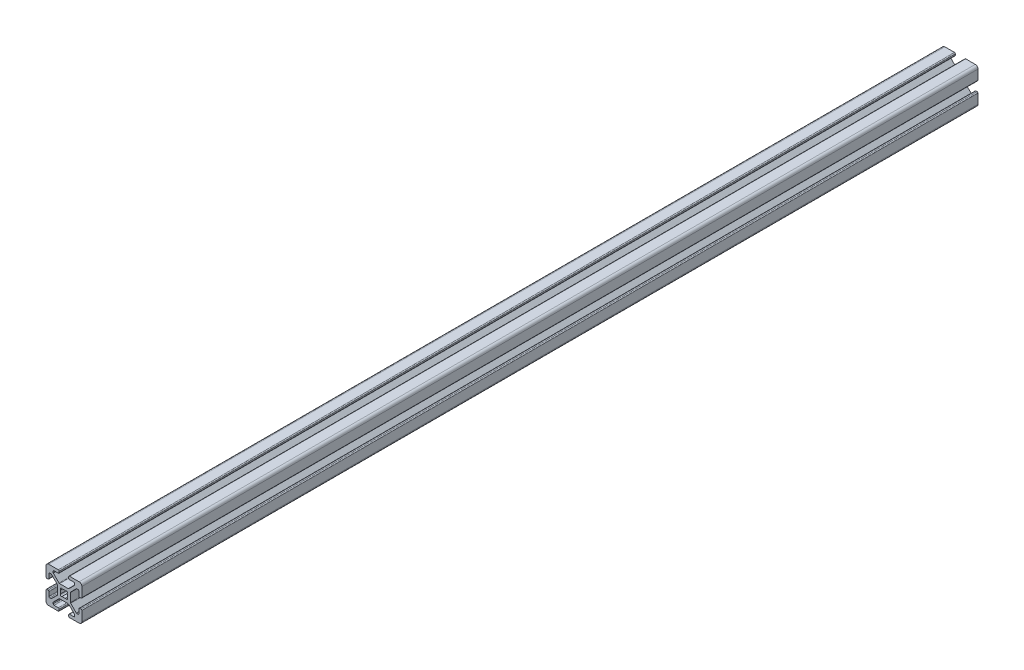
SolidWorks part; units mm, degrees
ref_plane "Front Plane" through (0, 0, 0) normal (0, 0, 1) x (1, 0, 0)
ref_plane "Top Plane" through (0, 0, 0) normal (0, 1, 0) x (1, 0, 0)
ref_plane "Right Plane" through (0, 0, 0) normal (1, 0, 0) x (0, 0, -1)
sketch "Sketch1" plane through (0, 0, 0) normal (0, 0, 1) x (1, 0, 0)
  line L0 (-2.7464, -3.807) -> (-5.848, -6.9086)
  line L1 (-8.5, -10) -> (-3.1319, -10)
  line L2 (-10, -8.5) -> (-10, -3.1319)
  line L3 (-8.5, 10) -> (-3.1319, 10)
  line L4 (10, -8.5) -> (10, -3.1319)
  line L6 (-10, 10) -> (-8.36, 8.36) construction
  line L7 (-2.3914, -3.66) -> (2.3914, -3.66)
  line L8 (-3.66, -2.3914) -> (-3.66, 2.3914)
  line L9 (-2.3914, 3.66) -> (2.3914, 3.66)
  line L10 (3.66, -2.3914) -> (3.66, 2.3914)
  line L13 (-5.4931, -8.36) -> (-3.1319, -8.36)
  line L14 (2.7464, -3.807) -> (5.848, -6.9086)
  line L15 (3.807, -2.7464) -> (6.9086, -5.848)
  line L16 (-5.995, -14.365) -> (5.995, -14.365)
  line L17 (2.63, -9.4981) -> (2.63, -8.8619)
  line L18 (8.8619, -2.63) -> (9.4981, -2.63)
  line L19 (5.995, -7.8581) -> (5.995, -7.2636)
  line L20 (-10, 3.1319) -> (-10, 8.5)
  line L22 (7.2636, -5.995) -> (7.8581, -5.995)
  line L23 (8.36, -5.4931) -> (8.36, -3.1319)
  line L24 (-3.807, -2.7464) -> (-6.9086, -5.848)
  line L25 (-9.4981, -2.63) -> (-8.8619, -2.63)
  line L26 (-7.8581, -5.995) -> (-7.2636, -5.995)
  line L27 (-5.995, -7.2636) -> (-5.995, -7.8581)
  line L28 (-2.63, -8.8619) -> (-2.63, -9.4981)
  line L30 (-5.4931, -8.36) -> (-3.1319, -8.36)
  line L31 (-3.807, 2.7464) -> (-6.9086, 5.848)
  line L32 (-2.7464, 3.807) -> (-5.848, 6.9086)
  line L33 (-2.63, 9.4981) -> (-2.63, 8.8619)
  line L34 (-5.995, 7.8581) -> (-5.995, 7.2636)
  line L35 (-7.2636, 5.995) -> (-7.8581, 5.995)
  line L36 (-8.8619, 2.63) -> (-9.4981, 2.63)
  line L37 (3.1319, 10) -> (8.5, 10)
  line L38 (-8.36, 5.4931) -> (-8.36, 3.1319)
  line L39 (2.7464, 3.807) -> (5.848, 6.9086)
  line L40 (3.807, 2.7464) -> (6.9086, 5.848)
  line L41 (9.4981, 2.63) -> (8.8619, 2.63)
  line L42 (7.8581, 5.995) -> (7.2636, 5.995)
  line L43 (5.995, 7.2636) -> (5.995, 7.8581)
  line L44 (2.63, 8.8619) -> (2.63, 9.4981)
  line L45 (8.36, -5.4931) -> (8.36, -3.1319)
  line L46 (5.4931, 8.36) -> (3.1319, 8.36)
  line L49 (-8.36, 5.4931) -> (-8.36, 3.1319)
  line L50 (5.4931, 8.36) -> (3.1319, 8.36)
  line L51 (-3.1319, 8.36) -> (-5.4931, 8.36)
  line L52 (-3.1319, 8.36) -> (-5.4931, 8.36)
  line L53 (10, 8.36) -> (8.36, 8.36) [skipped]
  line L54 (10, 3.1319) -> (10, 8.5)
  line L55 (8.36, 3.1319) -> (8.36, 5.4931)
  line L56 (8.36, 3.1319) -> (8.36, 5.4931)
  line L57 (3.1319, -8.36) -> (5.4931, -8.36)
  line L58 (3.1319, -8.36) -> (5.4931, -8.36)
  line L59 (3.1319, -10) -> (8.5, -10)
  line L60 (-8.36, -3.1319) -> (-8.36, -5.4931)
  line L61 (-8.36, -3.1319) -> (-8.36, -5.4931)
  line L62 (-8.36, 10) -> (-8.36, 8.36) [skipped]
  arc A0 (-8.5, -10) -> (-10, -8.5) centre (-8.5, -8.5) cw
  arc A1 (8.5, -10) -> (10, -8.5) centre (8.5, -8.5) ccw
  arc A2 (10, 8.5) -> (8.5, 10) centre (8.5, 8.5) ccw
  arc A3 (-8.5, 10) -> (-10, 8.5) centre (-8.5, 8.5) ccw
  arc A4 (10, -3.1319) -> (9.4981, -2.63) centre (9.4981, -3.1319) ccw
  arc A5 (8.8619, -2.63) -> (8.36, -3.1319) centre (8.8619, -3.1319) ccw
  arc A6 (7.8581, -5.995) -> (8.36, -5.4931) centre (7.8581, -5.4931) ccw
  arc A7 (7.2636, -5.995) -> (6.9086, -5.848) centre (7.2636, -5.4931) cw
  arc A8 (5.995, -7.2636) -> (5.848, -6.9086) centre (5.4931, -7.2636) ccw
  arc A9 (5.995, -7.8581) -> (5.4931, -8.36) centre (5.4931, -7.8581) cw
  arc A10 (3.1319, -10) -> (2.63, -9.4981) centre (3.1319, -9.4981) cw
  arc A11 (2.63, -8.8619) -> (3.1319, -8.36) centre (3.1319, -8.8619) cw
  arc A12 (-3.1319, -10) -> (-2.63, -9.4981) centre (-3.1319, -9.4981) ccw
  arc A13 (-2.63, -8.8619) -> (-3.1319, -8.36) centre (-3.1319, -8.8619) ccw
  arc A14 (-5.4931, -8.36) -> (-5.995, -7.8581) centre (-5.4931, -7.8581) cw
  arc A15 (-5.995, -7.2636) -> (-5.848, -6.9086) centre (-5.4931, -7.2636) cw
  arc A16 (-9.4981, -2.63) -> (-10, -3.1319) centre (-9.4981, -3.1319) ccw
  arc A17 (-8.36, -3.1319) -> (-8.8619, -2.63) centre (-8.8619, -3.1319) ccw
  arc A18 (-7.2636, -5.995) -> (-6.9086, -5.848) centre (-7.2636, -5.4931) ccw
  arc A19 (-7.8581, -5.995) -> (-8.36, -5.4931) centre (-7.8581, -5.4931) cw
  arc A20 (-3.807, -2.7464) -> (-3.66, -2.3914) centre (-4.1619, -2.3914) ccw
  arc A21 (-2.3914, -3.66) -> (-2.7464, -3.807) centre (-2.3914, -4.1619) ccw
  arc A22 (2.7464, -3.807) -> (2.3914, -3.66) centre (2.3914, -4.1619) ccw
  arc A23 (3.807, -2.7464) -> (3.66, -2.3914) centre (4.1619, -2.3914) cw
  arc A24 (9.4981, 2.63) -> (10, 3.1319) centre (9.4981, 3.1319) ccw
  arc A25 (8.8619, 2.63) -> (8.36, 3.1319) centre (8.8619, 3.1319) cw
  arc A26 (5.848, 6.9086) -> (5.995, 7.2636) centre (5.4931, 7.2636) ccw
  arc A27 (7.2636, 5.995) -> (6.9086, 5.848) centre (7.2636, 5.4931) ccw
  arc A28 (8.36, 5.4931) -> (7.8581, 5.995) centre (7.8581, 5.4931) ccw
  arc A29 (5.995, 7.8581) -> (5.4931, 8.36) centre (5.4931, 7.8581) ccw
  arc A30 (3.66, 2.3914) -> (3.807, 2.7464) centre (4.1619, 2.3914) cw
  arc A31 (-3.66, 2.3914) -> (-3.807, 2.7464) centre (-4.1619, 2.3914) ccw
  arc A32 (2.3914, 3.66) -> (2.7464, 3.807) centre (2.3914, 4.1619) ccw
  arc A33 (-2.3914, 3.66) -> (-2.7464, 3.807) centre (-2.3914, 4.1619) cw
  arc A34 (3.1319, 8.36) -> (2.63, 8.8619) centre (3.1319, 8.8619) cw
  arc A35 (2.63, 9.4981) -> (3.1319, 10) centre (3.1319, 9.4981) cw
  arc A36 (-9.4981, 2.63) -> (-10, 3.1319) centre (-9.4981, 3.1319) cw
  arc A37 (-8.8619, 2.63) -> (-8.36, 3.1319) centre (-8.8619, 3.1319) ccw
  arc A38 (-3.1319, 8.36) -> (-2.63, 8.8619) centre (-3.1319, 8.8619) ccw
  arc A39 (-2.63, 9.4981) -> (-3.1319, 10) centre (-3.1319, 9.4981) ccw
  arc A40 (-5.848, 6.9086) -> (-5.995, 7.2636) centre (-5.4931, 7.2636) cw
  arc A41 (-5.4931, 8.36) -> (-5.995, 7.8581) centre (-5.4931, 7.8581) ccw
  arc A42 (-6.9086, 5.848) -> (-7.2636, 5.995) centre (-7.2636, 5.4931) ccw
  arc A43 (-7.8581, 5.995) -> (-8.36, 5.4931) centre (-7.8581, 5.4931) ccw
  arc A44 (-1.7677, 0.9356) -> (-1.7677, -0.9356) centre (0, 0) ccw
  arc A45 (-0.9356, 1.7677) -> (-1.7677, 0.9356) centre (-1.4142, 1.4142) ccw
  arc A46 (1.7677, 0.9356) -> (0.9356, 1.7677) centre (1.4142, 1.4142) ccw
  arc A47 (0.9356, -1.7677) -> (1.7677, -0.9356) centre (1.4142, -1.4142) ccw
  arc A48 (-1.7677, -0.9356) -> (-0.9356, -1.7677) centre (-1.4142, -1.4142) ccw
  arc A49 (-0.9356, -1.7677) -> (0.9356, -1.7677) centre (0, 0) ccw
  arc A50 (1.7677, -0.9356) -> (1.7677, 0.9356) centre (0, 0) ccw
  arc A51 (0.9356, 1.7677) -> (-0.9356, 1.7677) centre (0, 0) ccw
  point P0 (0, 0)
  point P5 (0, 0)
  point P9 (-10, -10)
  point P11 (0, -10)
  point P14 (0, -3.66)
  point P23 (3.66, 0)
  point P66 (0, 0)
  point P70 (0, 0)
  dimension "D2" = 1.5
  dimension "D5" = 0.5019
  dimension "D6" = 4
  dimension "D7" = 1.19
  dimension "D1" = 20
  dimension "D3" = 11.99
  dimension "D4" = 4
  dimension "D8" = 4
extrude "Boss-Extrude1" add sketch "Sketch1" along normal blind 500 contours A43 L35 A42 L31 A31 L8 A20 L24 A18 L26 A19 L60 A17 L25 A16 L2 A0 L1 A12 L28 A13 L13 A14 L27 A15 L0 A21 L7 A22 L14 A8 L19 A9 L57 A11 L17 A10 L59 A1 L4 A4 L18 A5 L23 A6 L22 A7 L15 A23 L10 A30
